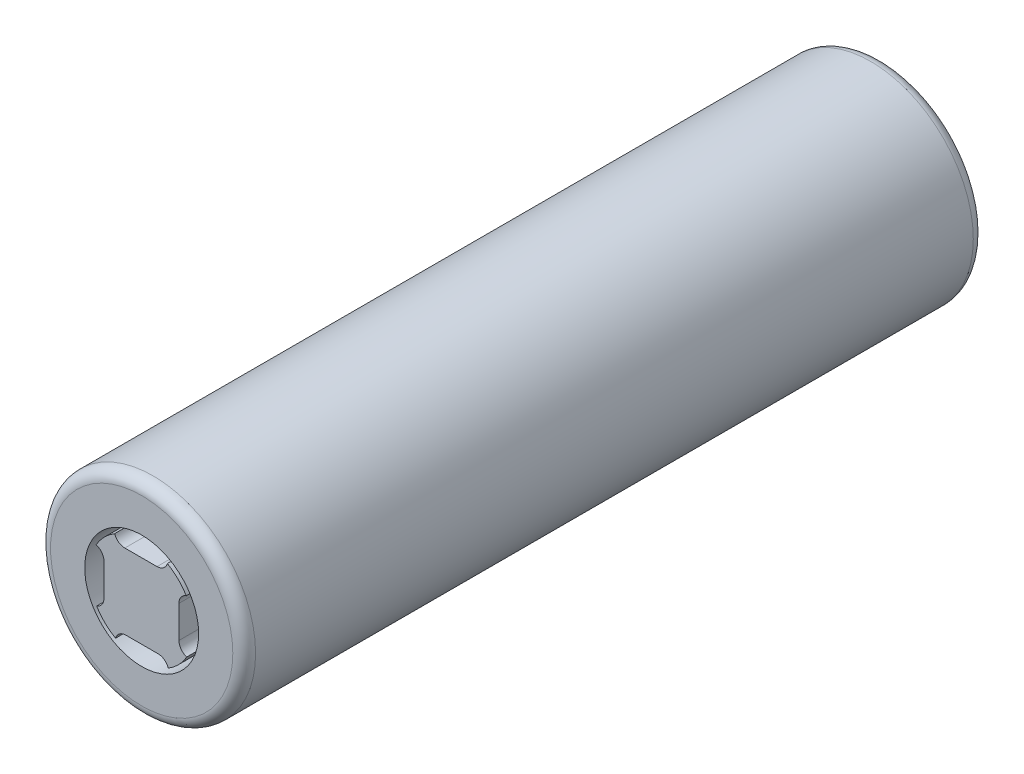
SolidWorks part; units mm, degrees
ref_plane "Front Plane" through (0, 0, 0) normal (0, 0, 1) x (1, 0, 0)
ref_plane "Top Plane" through (0, 0, 0) normal (0, 1, 0) x (1, 0, 0)
ref_plane "Right Plane" through (0, 0, 0) normal (1, 0, 0) x (0, 0, -1)
sketch "Sketch1" plane through (0, 0, 0) normal (0, 0, 1) x (1, 0, 0)
  circle A0 centre (0, 0) radius 9
  dimension "D1" = 18
extrude "Boss-Extrude1" add sketch "Sketch1" against normal blind 65
fillet "Fillet3" radius 1 2 edges at (9, 0, 0) (9, 0, -65)
sketch "Sketch2" plane through (0, 0, -65) normal (0, 0, -1) x (-1, 0, 0)
  circle A0 centre (0, 0) radius 6.5
  dimension "D1" = 13
extrude "Cut-Extrude1" cut sketch "Sketch2" against normal blind 0.02
sketch "Sketch3" plane through (0, 0, 0) normal (0, 0, 1) x (1, 0, 0)
  circle A0 centre (0, 0) radius 5
  dimension "D1" = 10
extrude "Cut-Extrude2" cut sketch "Sketch3" against normal blind 3
sketch "Sketch5" plane through (0, 0, -3) normal (0, 0, 1) x (1, 0, 0)
  line L1 (-1.3644, -3.2897) -> (1.4586, -3.2897)
  line L3 (0, 0) -> (3.2897, 0) construction
  line L4 (0, 0) -> (-4.5823, 0) construction
  line L5 (0, 0) -> (0, 4.5823) construction
  line L7 (-3.2897, 1.3644) -> (-3.2897, -1.4586)
  line L10 (1.3644, 3.2897) -> (-1.4586, 3.2897)
  line L13 (3.2897, -1.3644) -> (3.2897, 1.4586)
  line L22 (4.2365, 0) -> (4.5823, 0) construction
  arc A0 (-3.931, -2.3548) -> (-2.2751, -3.9776) centre (0, 0) ccw
  arc A1 (-1.3644, -3.2897) -> (-2.2751, -3.9776) centre (-1.3644, -4.2365) ccw
  arc A2 (2.3548, -3.931) -> (1.4586, -3.2897) centre (1.4586, -4.2365) ccw
  arc A3 (-3.931, -2.3548) -> (-2.2751, -3.9776) centre (0, 0) ccw
  arc A4 (-3.2897, 1.3644) -> (-3.9776, 2.2751) centre (-4.2365, 1.3644) ccw
  arc A5 (-3.931, -2.3548) -> (-3.2897, -1.4586) centre (-4.2365, -1.4586) ccw
  arc A6 (-3.931, -2.3548) -> (-2.2751, -3.9776) centre (0, 0) ccw
  arc A7 (1.3644, 3.2897) -> (2.2751, 3.9776) centre (1.3644, 4.2365) ccw
  arc A8 (-2.3548, 3.931) -> (-1.4586, 3.2897) centre (-1.4586, 4.2365) ccw
  arc A9 (-3.931, -2.3548) -> (-2.2751, -3.9776) centre (0, 0) ccw
  arc A10 (3.2897, -1.3644) -> (3.9776, -2.2751) centre (4.2365, -1.3644) ccw
  arc A11 (3.931, 2.3548) -> (3.2897, 1.4586) centre (4.2365, 1.4586) ccw
  arc A16 (-2.3548, 3.931) -> (-3.9776, 2.2751) centre (0, 0) ccw
  arc A17 (-2.3548, 3.931) -> (-3.9776, 2.2751) centre (0, 0) ccw
  arc A18 (-2.3548, 3.931) -> (-3.9776, 2.2751) centre (0, 0) ccw
  arc A19 (-2.3548, 3.931) -> (-3.9776, 2.2751) centre (0, 0) ccw
  arc A22 (3.931, 2.3548) -> (2.2751, 3.9776) centre (0, 0) ccw
  arc A23 (3.931, 2.3548) -> (2.2751, 3.9776) centre (0, 0) ccw
  arc A24 (3.931, 2.3548) -> (2.2751, 3.9776) centre (0, 0) ccw
  arc A25 (3.931, 2.3548) -> (2.2751, 3.9776) centre (0, 0) ccw
  arc A26 (2.3548, -3.931) -> (3.9776, -2.2751) centre (0, 0) ccw
  arc A27 (2.3548, -3.931) -> (3.9776, -2.2751) centre (0, 0) ccw
  arc A28 (2.3548, -3.931) -> (3.9776, -2.2751) centre (0, 0) ccw
  arc A29 (2.3548, -3.931) -> (3.9776, -2.2751) centre (0, 0) ccw
  point P5 (0.0471, -4.2365)
  point P15 (-4.2365, -0.0471)
  point P19 (-4.2365, -0.0471)
  point P23 (-0.0471, 4.2365)
  point P27 (-0.0471, 4.2365)
  point P35 (4.2365, 0.0471)
  point P49 (4.2365, 0.0471)
  dimension "D1" = 4
extrude "Boss-Extrude2" add sketch "Sketch5" along normal blind 3.02 contours A2 A26 A10 L13 A11 A22 A7 L10 A8 A16 A4 L7 A5 A0 A1 L1
